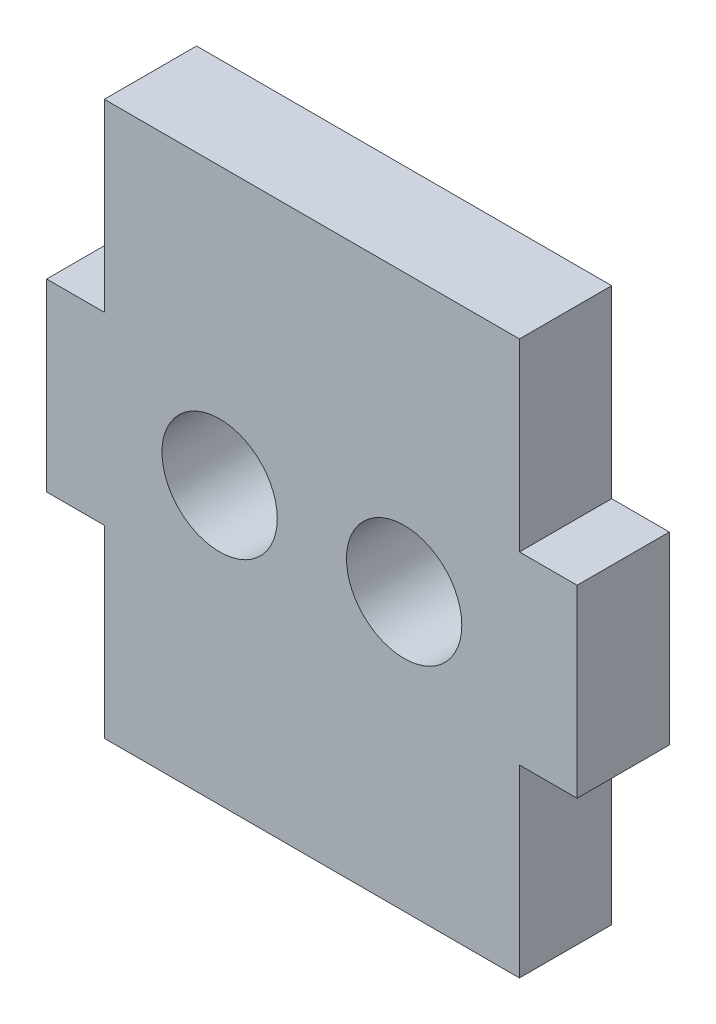
SolidWorks part; units mm, degrees
ref_plane "Front Plane" through (0, 0, 0) normal (0, 0, 1) x (1, 0, 0)
ref_plane "Top Plane" through (0, 0, 0) normal (0, 1, 0) x (1, 0, 0)
ref_plane "Right Plane" through (0, 0, 0) normal (1, 0, 0) x (0, 0, -1)
sketch "Model" plane through (0, 0, 0) normal (0, 0, 1) x (1, 0, 0)
  line L0 (5.7504, 12) -> (5.7504, 0) construction
  line L37 (1.25, 4) -> (0, 4)
  line L38 (10.2507, 4) -> (11.5007, 4)
  line L39 (1.25, 0) -> (10.2507, 0)
  line L40 (1.25, 4) -> (1.25, 0)
  line L41 (10.2507, 4) -> (10.2507, 0)
  line L126 (10.2507, 8) -> (11.5007, 8)
  line L127 (1.25, 8) -> (0, 8)
  line L128 (10.2507, 12) -> (1.25, 12)
  line L129 (10.2507, 8) -> (10.2507, 12)
  line L130 (1.25, 8) -> (1.25, 12)
  line L131 (0, 8) -> (0, 4)
  line L132 (11.5007, 8) -> (11.5007, 4)
  circle A81 centre (7.7507, 6) radius 1.25
  circle A82 centre (3.75, 6) radius 1.25
  dimension "D1" = 2.5
  dimension "D2" = 2
  dimension "D3" = 2.5
  dimension "D4" = 9.0007
  dimension "D5" = 4
  dimension "D6" = 2.5
extrude "Boss-Extrude1" add sketch "Model" along normal blind 2
equation "\"D4@Model\"= \"fingerWidth@parametersSketch@prostheticParameters.SLDPRT\" * 0.5556"
